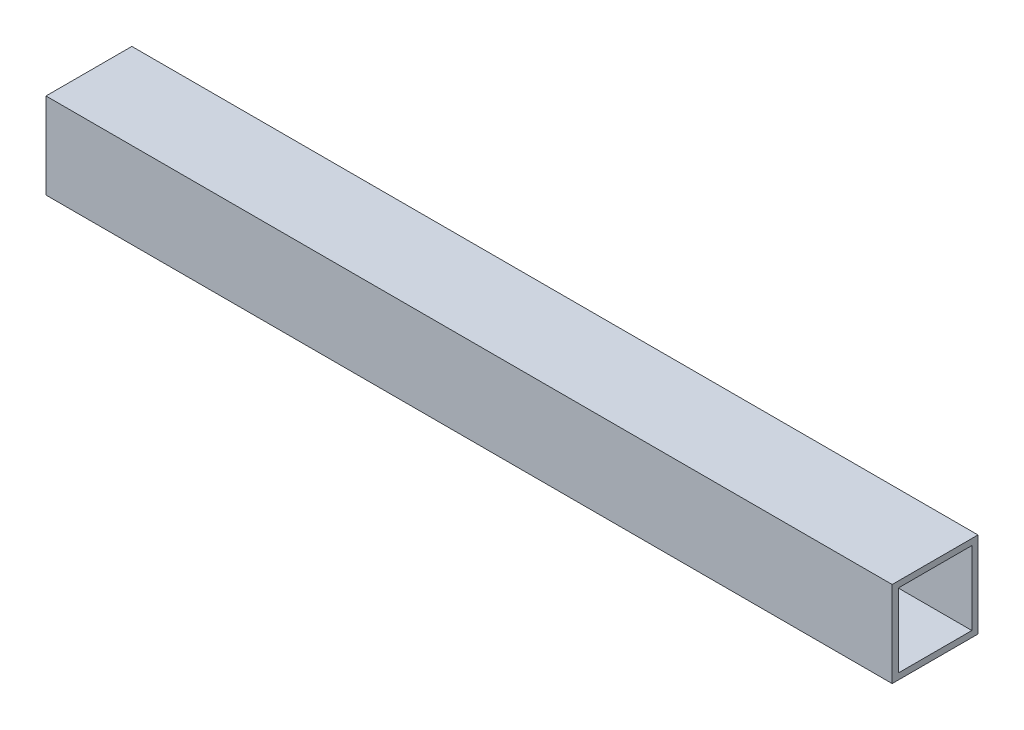
SolidWorks part; units mm, degrees
material "6061 Alloy"
ref_plane "Front Plane" through (0, 0, 0) normal (0, 0, 1) x (1, 0, 0)
ref_plane "Top Plane" through (0, 0, 0) normal (0, 1, 0) x (1, 0, 0)
ref_plane "Right Plane" through (0, 0, 0) normal (1, 0, 0) x (0, 0, -1)
sketch "Sketch1" plane through (0, 0, 0) normal (1, 0, 0) x (0, 0, -1)
  line L1 (0, 0) -> (44.45, 0)
  line L2 (0, 0) -> (0, 44.45)
  line L3 (0, 44.45) -> (44.45, 44.45)
  line L4 (44.45, 0) -> (44.45, 44.45)
  line L5 (3.175, 41.275) -> (41.275, 41.275)
  line L6 (3.175, 41.275) -> (3.175, 3.175)
  line L7 (3.175, 3.175) -> (41.275, 3.175)
  line L8 (41.275, 41.275) -> (41.275, 3.175)
  dimension "D1" = 44.45
  dimension "D2" = 38.1
  dimension "D3" = 44.45
  dimension "D4" = 38.1
  dimension "D5" = 3.175
  dimension "D6" = 3.175
extrude "Boss-Extrude1" add sketch "Sketch1" along normal blind 438.15
sketch "Sketch2" plane through (0, 44.45, 0) normal (0, 1, 0) x (1, 0, 0)
  line L0 (0, 44.45) -> (0, 0)
  line L1 (0, 0) -> (76.9897, 0)
  line L2 (438.15, 0) -> (0, 0) construction
  line L3 (76.9897, 0) -> (0, 44.45)
  line L4 (438.15, 44.45) -> (412.4868, 0)
  line L5 (412.4868, 0) -> (438.15, 0)
  line L6 (438.15, 0) -> (438.15, 44.45)
  dimension "D1" = 30
  dimension "D2" = 60
